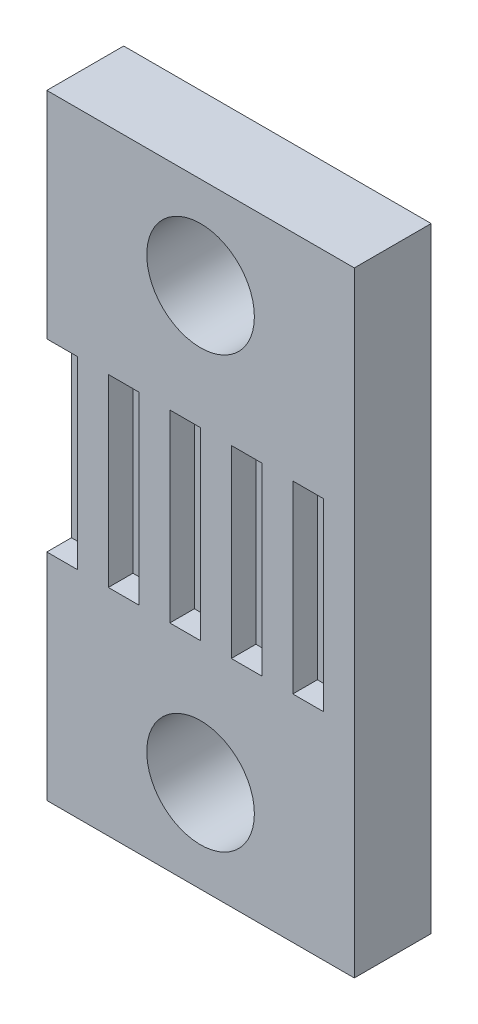
SolidWorks part; units mm, degrees
ref_plane "Спереди" through (0, 0, 0) normal (0, 0, 1) x (1, 0, 0)
ref_plane "Сверху" through (0, 0, 0) normal (0, 1, 0) x (1, 0, 0)
ref_plane "Справа" through (0, 0, 0) normal (1, 0, 0) x (0, 0, -1)
sketch "Эскиз1" plane through (0, 0, 0) normal (0, 0, 1) x (1, 0, 0)
  line L0 (5, 20) -> (5, 0) construction
  line L1 (0, 0) -> (10, 0)
  line L2 (0, 0) -> (0, 20)
  line L3 (0, 20) -> (10, 20)
  line L4 (10, 0) -> (10, 20)
  circle A0 centre (5, 17) radius 1.75
  circle A1 centre (5, 3) radius 1.75
  dimension "D3" = 3
  dimension "D4" = 3
  dimension "D5" = 3.5
  dimension "D1" = 10
  dimension "D2" = 20
extrude "Бобышка-Вытянуть1" add sketch "Эскиз1" along normal blind 2.5
sketch "Эскиз2" plane through (0, 0, 2.5) normal (0, 0, 1) x (1, 0, 0)
  line L0 (0, 20) -> (0, 0) construction
  line L1 (0, 13) -> (1, 13)
  line L2 (0, 13) -> (0, 7)
  line L3 (0, 7) -> (1, 7)
  line L4 (1, 13) -> (1, 7)
  line L5 (1, 10) -> (10, 10) construction
  line L6 (10, 0) -> (10, 20) construction
  line L7 (2, 13) -> (3, 13)
  line L8 (2, 13) -> (2, 7)
  line L9 (3, 13) -> (3, 7)
  line L10 (2, 7) -> (3, 7)
  line L11 (4, 13) -> (5, 13)
  line L12 (4, 13) -> (4, 7)
  line L13 (5, 13) -> (5, 7)
  line L14 (4, 7) -> (5, 7)
  line L15 (6, 13) -> (7, 13)
  line L16 (6, 13) -> (6, 7)
  line L17 (7, 13) -> (7, 7)
  line L18 (6, 7) -> (7, 7)
  line L19 (8, 13) -> (9, 13)
  line L20 (8, 13) -> (8, 7)
  line L21 (9, 13) -> (9, 7)
  line L22 (8, 7) -> (9, 7)
  dimension "D1" = 6
  dimension "D2" = 1
  dimension "D3" = 5
extrude "Вырез-Вытянуть1" cut sketch "Эскиз2" against normal blind 0.8
